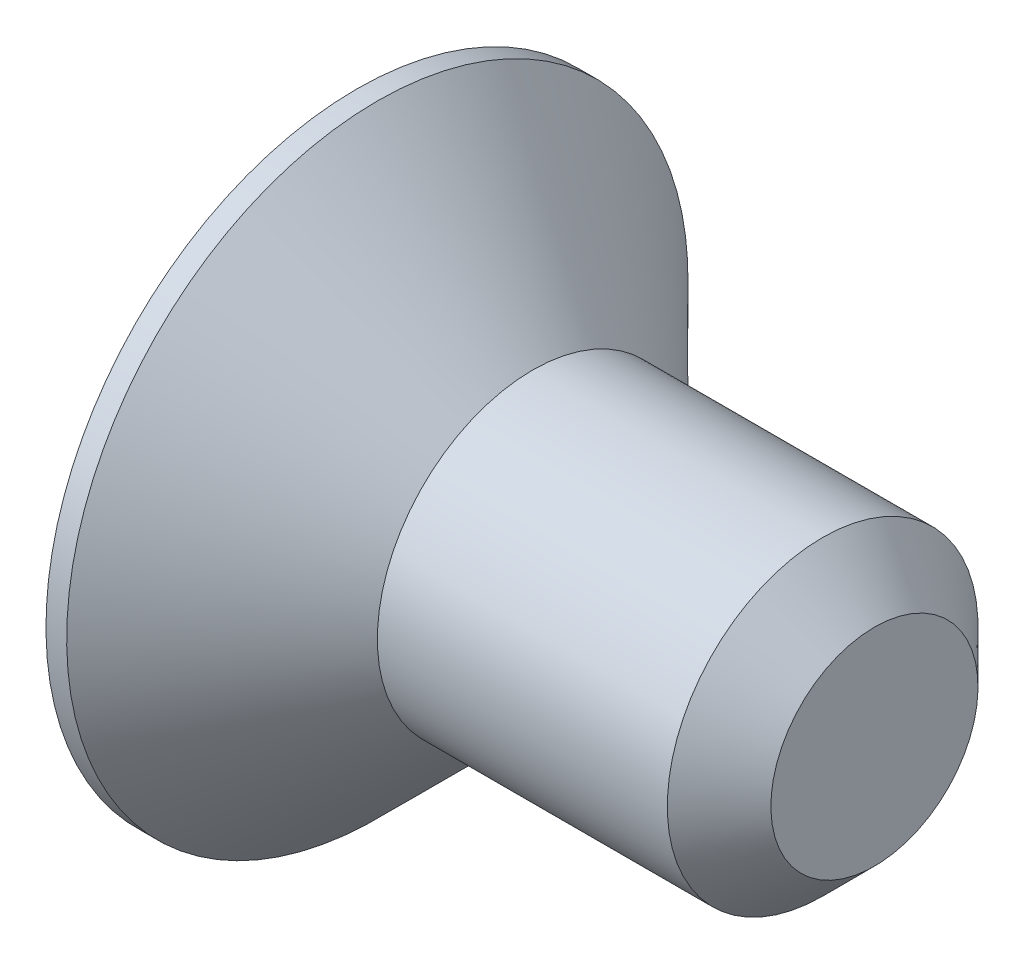
SolidWorks part; units mm, degrees
ref_plane "Plan de face" through (0, 0, 0) normal (0, 0, 1) x (1, 0, 0)
ref_plane "Plan de dessus" through (0, 0, 0) normal (0, 1, 0) x (1, 0, 0)
ref_plane "Plan de droite" through (0, 0, 0) normal (1, 0, 0) x (0, 0, -1)
sketch "Esquisse1" plane through (0, 0, 0) normal (0, 0, 1) x (1, 0, 0)
  line L0 (0, 0) -> (0, 3)
  line L1 (0, 3) -> (0.2, 3)
  line L2 (0.2, 3) -> (1.7, 1.5)
  line L3 (1.7, 1.5) -> (5, 1.5)
  line L4 (5, 1.5) -> (5, 0)
  line L5 (5, 0) -> (0, 0) construction
  line L6 (0, 0) -> (5, 0)
  dimension "D1" = 1.7
  dimension "D2" = 5
  dimension "D3" = 3
  dimension "D4" = 6
  dimension "D5" = 45
revolve "Révolution1" add sketch "Esquisse1" angle 360 about L5
chamfer "Chanfrein1" distance 0.5 angle 45 1 edges at (5, 1.5, 0)
sketch "Esquisse2" plane through (0, 0, 0) normal (-1, 0, 0) x (0, 0, 1)
  line L1 (0, 1.1547) -> (-1, 0.5774)
  line L2 (-1, 0.5774) -> (-1, -0.5774)
  line L3 (-1, -0.5774) -> (0, -1.1547)
  line L4 (0, -1.1547) -> (1, -0.5774)
  line L5 (1, -0.5774) -> (1, 0.5774)
  line L6 (1, 0.5774) -> (0, 1.1547)
  circle A0 centre (0, 0) radius 1 construction
  dimension "D1" = 2
extrude "Enlèv. mat.-Extru.1" cut sketch "Esquisse2" against normal blind 1.2
